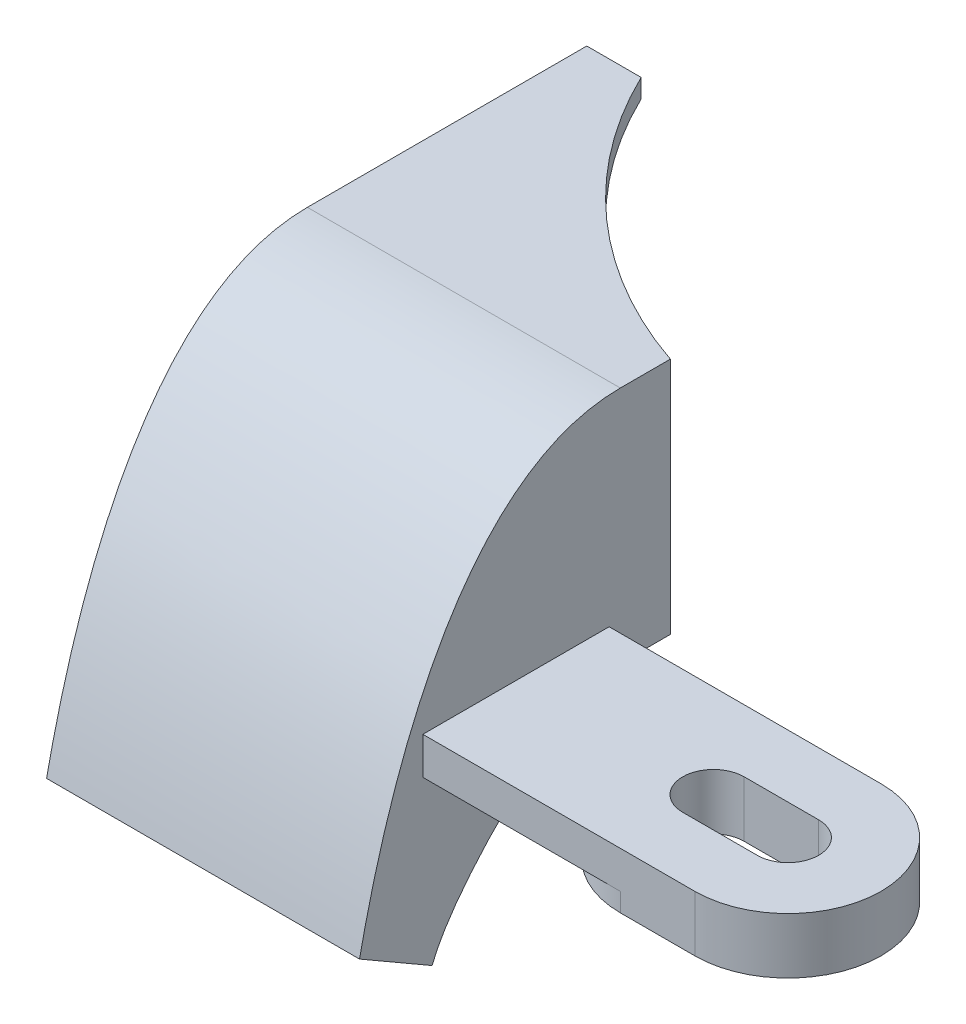
SolidWorks part; units mm, degrees
ref_plane "Plano frontal" through (0, 0, 0) normal (0, 0, 1) x (1, 0, 0)
ref_plane "Plano superior" through (0, 0, 0) normal (0, 1, 0) x (1, 0, 0)
ref_plane "Plano direito" through (0, 0, 0) normal (1, 0, 0) x (0, 0, -1)
sketch "Esboço1" plane through (0, 0, 0) normal (0, 0, 1) x (1, 0, 0)
  line L1 (-8.4, 6.4) -> (8.4, 6.4)
  line L2 (-8.4, 6.4) -> (-8.4, -6.4)
  line L3 (-8.4, -6.4) -> (8.4, -6.4)
  line L4 (8.4, 6.4) -> (8.4, -6.4)
  line L5 (-8.4, 6.4) -> (8.4, -6.4) construction
  line L6 (-8.4, -6.4) -> (8.4, 6.4) construction
  point P0 (0, 0)
  dimension "D1" = 12.8
  dimension "D2" = 16.8
extrude "Ressalto-extrusão1" add sketch "Esboço1" along normal blind 15
sketch "Esboço2" plane through (8.4, 0, 0) normal (1, 0, 0) x (0, 0, -1)
  line L0 (-15, -6.4) -> (0, -6.4) construction
  line L1 (-18.6376, -6.4) -> (-11.3604, -6.4) construction
  line L2 (-25.1029, -15.4) -> (-29, -13.15)
  line L3 (-15, 6.4) -> (-15, -6.4)
  line L6 (-15, 6.4) -> (0, 6.4) construction
  line L7 (-21.1788, 6.4) -> (-8.8176, 6.4) construction
  spline S0 degree 3 poles (-15, 6.4) (-24.57, 6.4) (-28.0693, -8.7492) (-29, -13.15) knots 0 0 0 0 1 1 1 1
  spline S1 degree 3 poles (-15, -6.4) (-18.0322, -6.4) (-23.9448, -12.2979) (-25.1029, -15.4) knots 0 0 0 0 1 1 1 1
  point P11 (-24.1238, -13.0066)
  point P12 (0, 0)
  point P14 (-29, -10.4256)
  point P19 (-29, -16.4774)
  dimension "D1" = 14
  dimension "D2" = 9
  dimension "D3" = 4.5
  dimension "D4" = 30
extrude "Ressalto-extrusão2" add sketch "Esboço2" against normal through all
shell "Casca1" thickness 1
sketch "Esboço5" plane through (0, 6.4, 0) normal (0, 1, 0) x (1, 0, 0)
  circle A0 centre (16.15, 10.4) radius 24
  dimension "D1" = 48
  dimension "D2" = 7.75
  dimension "D3" = 10.4
extrude "Corte-extrusão1" cut sketch "Esboço5" against normal through all
sketch "Esboço6" plane through (0, -6.4, 0) normal (0, -1, 0) x (1, 0, 0)
  line L0 (23, 25.6) -> (8.4, 25.6)
  line L1 (8.4, 15) -> (8.4, 29) construction
  line L2 (8.4, 25.6) -> (8.4, 15.6)
  line L3 (8.4, 15.6) -> (23, 15.6)
  line L4 (19, 22.25) -> (23, 22.25)
  line L6 (19, 18.95) -> (23, 18.95)
  arc A0 (23, 18.95) -> (23, 22.25) centre (23, 20.6) ccw
  arc A1 (23, 15.6) -> (23, 25.6) centre (23, 20.6) ccw
  arc A2 (19, 22.25) -> (19, 18.95) centre (19, 20.6) ccw
  dimension "D1" = 3.3
  dimension "D4" = 5
  dimension "D2" = 20.6
  dimension "D3" = 23
  dimension "D5" = 4
extrude "Ressalto-extrusão3" add sketch "Esboço6" against normal blind 2
sketch "Esboço7" plane through (0, -6.4, 0) normal (0, -1, 0) x (1, 0, 0)
  line L0 (19, 18.95) -> (23, 18.95) construction
  line L1 (23, 22.25) -> (19, 22.25) construction
  line L2 (19, 18.95) -> (23, 18.95)
  line L3 (23, 22.25) -> (19, 22.25)
  line L4 (19, 20.6) -> (23, 20.6) construction
  line L5 (19, 25.6) -> (23, 25.6)
  line L6 (19, 15.6) -> (23, 15.6)
  arc A0 (19, 22.25) -> (19, 18.95) centre (19, 20.6) ccw construction
  arc A1 (23, 18.95) -> (23, 22.25) centre (23, 20.6) ccw construction
  arc A5 (19, 22.25) -> (19, 18.95) centre (19, 20.6) ccw
  arc A6 (23, 18.95) -> (23, 22.25) centre (23, 20.6) ccw
  arc A7 (19, 25.6) -> (19, 15.6) centre (19, 20.6) ccw
  arc A8 (23, 15.6) -> (23, 25.6) centre (23, 20.6) ccw
  arc A9 (23, 15.6) -> (23, 25.6) centre (23, 20.6) ccw construction
  point P6 (21, 20.6)
extrude "Ressalto-extrusão4" add sketch "Esboço7" along normal blind 1
